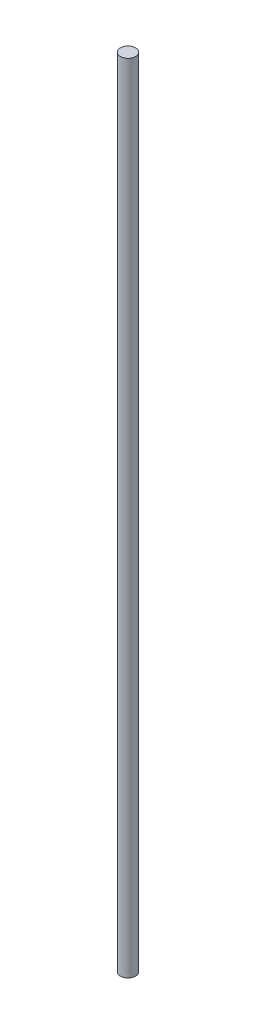
SolidWorks part; units mm, degrees
ref_plane "Front Plane" through (0, 0, 0) normal (0, 0, 1) x (1, 0, 0)
ref_plane "Top Plane" through (0, 0, 0) normal (0, 1, 0) x (1, 0, 0)
ref_plane "Right Plane" through (0, 0, 0) normal (1, 0, 0) x (0, 0, -1)
sketch "Sketch1" plane through (0, 0, 0) normal (0, 1, 0) x (1, 0, 0)
  circle A0 centre (0, 0) radius 2
  dimension "D1" = 4
extrude "Boss-Extrude1" add sketch "Sketch1" along normal blind 210
